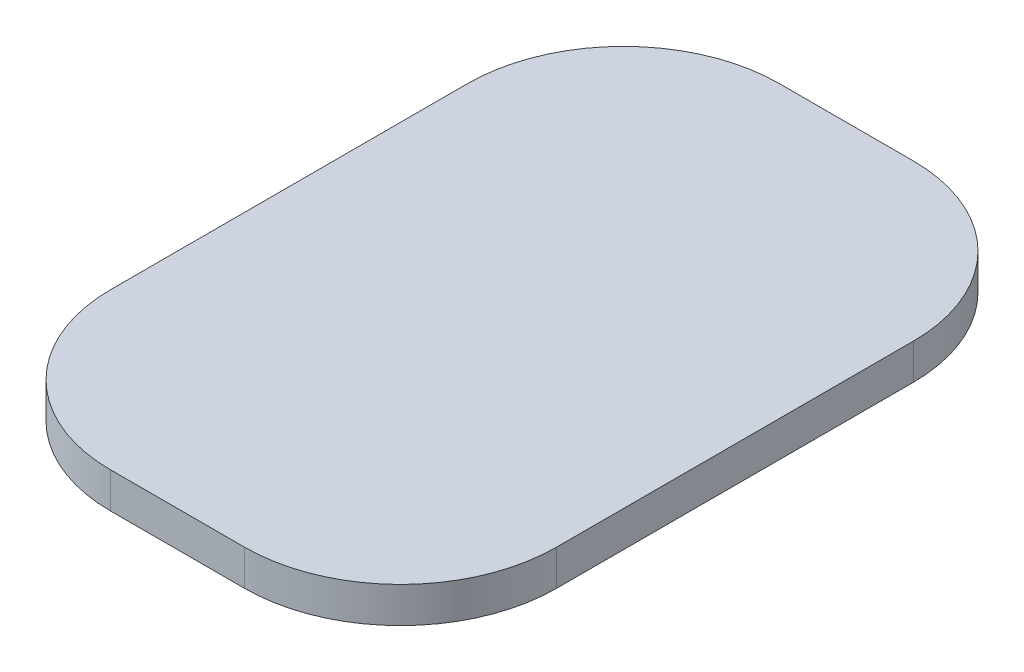
SolidWorks part; units mm, degrees
ref_plane "Front Plane" through (0, 0, 0) normal (0, 0, 1) x (1, 0, 0)
ref_plane "Top Plane" through (0, 0, 0) normal (0, 1, 0) x (1, 0, 0)
ref_plane "Right Plane" through (0, 0, 0) normal (1, 0, 0) x (0, 0, -1)
sketch "Sketch1" plane through (0, 0, 0) normal (0, 1, 0) x (1, 0, 0)
  line L1 (-78.3383, 69.6588) -> (21.6617, 69.6588)
  line L2 (-78.3383, 69.6588) -> (-78.3383, -80.3412)
  line L3 (-78.3383, -80.3412) -> (21.6617, -80.3412)
  line L4 (21.6617, 69.6588) -> (21.6617, -80.3412)
  dimension "D1" = 150
  dimension "D2" = 100
extrude "Boss-Extrude1" add sketch "Sketch1" along normal blind 8
fillet "Fillet1" radius 35 4 edges at (-78.3383, 4, -69.6588) (21.6617, 4, -69.6588) (-78.3383, 4, 80.3412) (21.6617, 4, 80.3412)
sketch "Sketch2" plane through (0, 8, 0) normal (0, 1, 0) x (1, 0, 0)
  line L0 (-28.3383, 69.6588) -> (-28.3383, -80.3412) construction
  line L1 (-13.3383, 69.6588) -> (-43.3383, 69.6588) construction
  line L2 (-43.3383, -80.3412) -> (-13.3383, -80.3412) construction
  line L3 (-78.3383, -5.3412) -> (21.6617, -5.3412) construction
  line L4 (-78.3383, 34.6588) -> (-78.3383, -45.3412) construction
  line L5 (21.6617, -45.3412) -> (21.6617, 34.6588) construction
  circle A0 centre (-28.3383, 12.9461) radius 2
